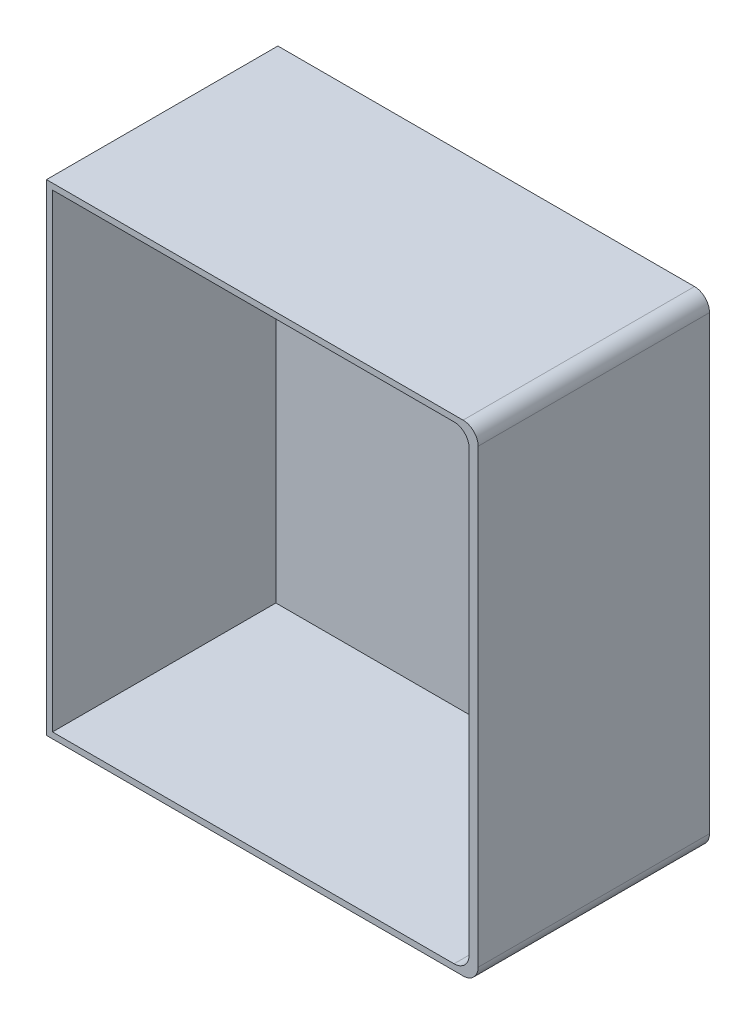
SolidWorks part; units mm, degrees
ref_plane "Спереди" through (0, 0, 0) normal (0, 0, 1) x (1, 0, 0)
ref_plane "Сверху" through (0, 0, 0) normal (0, 1, 0) x (1, 0, 0)
ref_plane "Справа" through (0, 0, 0) normal (1, 0, 0) x (0, 0, -1)
sketch "Эскиз1" plane through (0, 0, 0) normal (0, 0, 1) x (1, 0, 0)
  line L0 (43, -47.95) -> (43, 47.95)
  line L1 (43, 47.95) -> (-43, 47.95)
  line L2 (-43, 47.95) -> (-43, -47.95)
  line L3 (-43, -47.95) -> (43, -47.95)
  line L4 (-43, 47.95) -> (43, -47.95) construction
  point P4 (0, 0)
  dimension "D1" = 86
  dimension "D2" = 95.9
extrude "Бобышка-Вытянуть1" add sketch "Эскиз1" along normal blind 46.1
sketch "Эскиз2" plane through (0, 0, 0) normal (0, 0, 1) x (1, 0, 0)
  line L0 (-43, 47.95) -> (-43, -47.95) construction
  line L1 (-43, 42.95) -> (-43, 35.8706)
  line L2 (-43, -42.95) -> (-43, -35.8706)
  line L3 (-43, 0) -> (43, 0) construction
  line L4 (43, -47.95) -> (43, 47.95) construction
  arc A0 (-43, -42.95) -> (-43, 42.95) centre (14.4749, 0) cw
  arc A1 (-43, 35.8706) -> (-43, -35.8706) centre (14.4749, 0) ccw
  point P13 (-53.2751, 0)
  dimension "D3" = 67.75
  dimension "D1" = 5
  dimension "D2" = 5
  dimension "D4" = 4
  dimension "D5" = 10.2751
extrude "Бобышка-Вытянуть2" add sketch "Эскиз2" along normal blind 5
sketch "Эскиз3" plane through (0, 0, 46.1) normal (0, 0, 1) x (1, 0, 0)
  line L5 (41.2, -47.95) -> (41.2, 47.95)
  line L6 (-41.8, -46.75) -> (43, -46.75)
  line L7 (-41.8, 46.75) -> (-41.8, -46.75)
  line L8 (43, 46.75) -> (-41.8, 46.75)
  line L9 (-41.8, -46.75) -> (41.2, -46.75)
  line L10 (-41.8, 46.75) -> (-41.8, -46.75)
  line L11 (41.2, 46.75) -> (-41.8, 46.75)
  line L12 (41.2, -46.75) -> (41.2, 46.75)
  dimension "D1" = 1.2
  dimension "D2" = 1.8
extrude "Вырез-Вытянуть1" cut sketch "Эскиз3" against normal offset from surface 1.6 up to face at (-48.1376, 0, 0)
fillet "Скругление1" radius 3 4 edges at (43, -47.95, 23.05) (43, 47.95, 23.05) (41.2, -46.75, 23.85) (41.2, 46.75, 23.85)
equation "\"D1@Эскиз2\"=\"D2@Эскиз2\""
